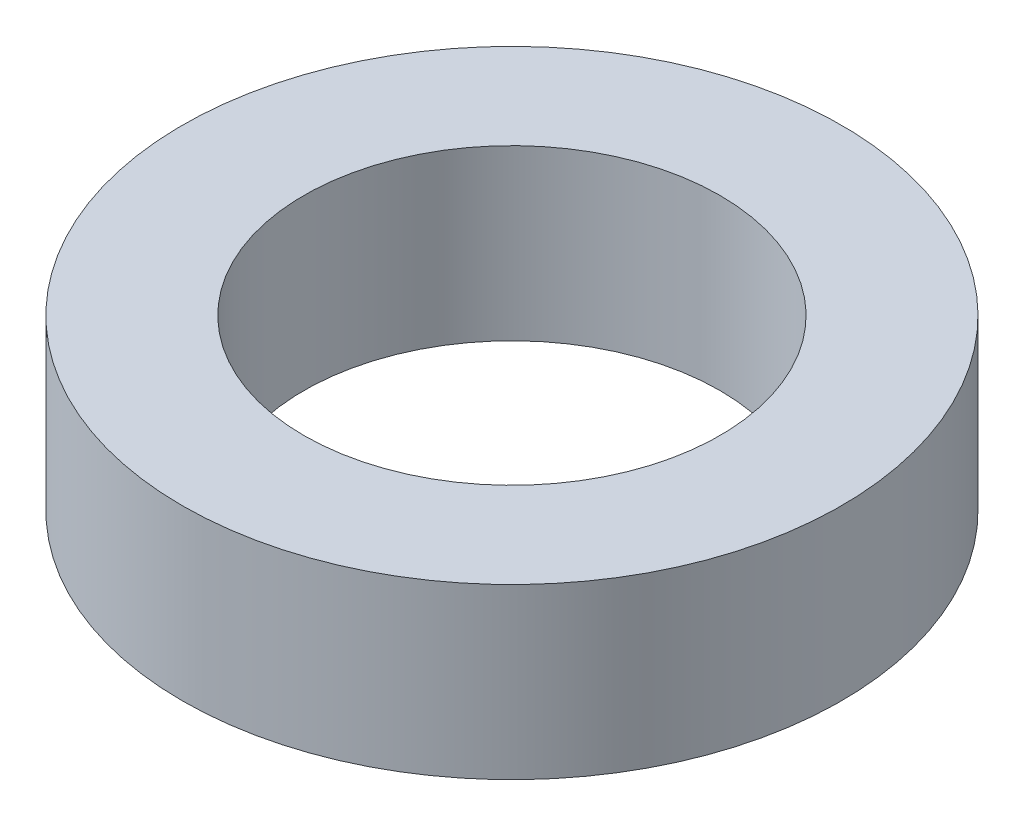
SolidWorks part; units mm, degrees
ref_plane "Front Plane" through (0, 0, 0) normal (0, 0, 1) x (1, 0, 0)
ref_plane "Top Plane" through (0, 0, 0) normal (0, 1, 0) x (1, 0, 0)
ref_plane "Right Plane" through (0, 0, 0) normal (1, 0, 0) x (0, 0, -1)
sketch "Sketch1" plane through (0, 0, 0) normal (0, 1, 0) x (1, 0, 0)
  line L0 (0, 0) -> (-25.35, 0) construction
  circle A0 centre (0, 0) radius 16
  circle A1 centre (0, 0) radius 25.35
extrude "Boss-Extrude1" add sketch "Sketch1" along normal blind 13
